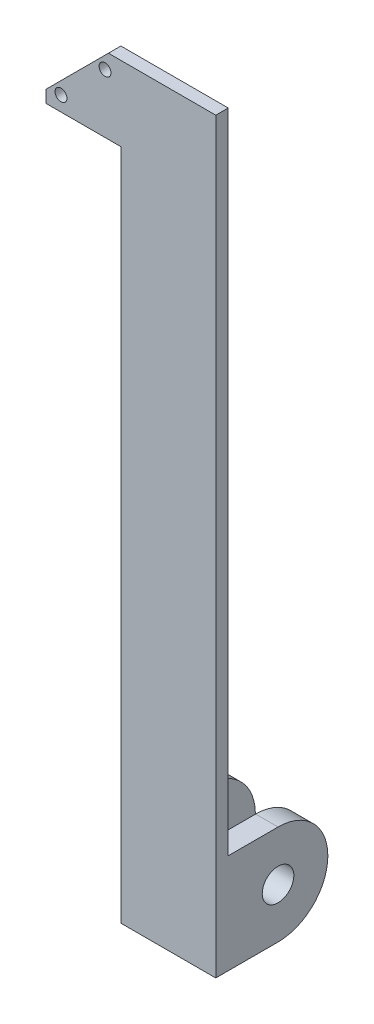
SolidWorks part; units mm, degrees
ref_plane "Front Plane" through (0, 0, 0) normal (0, 0, 1) x (1, 0, 0)
ref_plane "Top Plane" through (0, 0, 0) normal (0, 1, 0) x (1, 0, 0)
ref_plane "Right Plane" through (0, 0, 0) normal (1, 0, 0) x (0, 0, -1)
sketch "Sketch1" plane through (0, 0, 0) normal (0, 0, 1) x (1, 0, 0)
  line L0 (-30, 270) -> (0, 300)
  line L1 (0, 0) -> (38.1, 0)
  line L2 (0, 0) -> (0, 300)
  line L3 (0, 300) -> (38.1, 300)
  line L4 (38.1, 0) -> (38.1, 300)
  line L5 (0, 300) -> (-30, 300)
  line L6 (0, 300) -> (0, 270)
  line L7 (0, 270) -> (-30, 270)
  line L8 (-30, 300) -> (-30, 270)
  line L9 (-30, 275) -> (-5, 300)
  circle A0 centre (-6.364, 293.636) radius 2.3813
  circle A1 centre (-24.0416, 275.9584) radius 2.3813
  dimension "D5" = 4.7625
  dimension "D6" = 4.7625
  dimension "D1" = 300
  dimension "D2" = 38.1
  dimension "D3" = 30
  dimension "D4" = 30
  dimension "D7" = 25
  dimension "D8" = 9
  dimension "D9" = 5
  dimension "D10" = 5
extrude "Boss-Extrude1" add sketch "Sketch1" along normal blind 5 contours A1 L0 A0 L5 L9 L8 | A1 L0 L7 L2 A0 | L1 L4 L3 L2
sketch "Sketch4" plane through (0, 0, 0) normal (0, 0, -1) x (-1, 0, 0)
  line L0 (0, 0) -> (0, 270) construction
  line L1 (-38.1, 0) -> (0, 0)
  line L2 (-38.1, 0) -> (-38.1, 40)
  line L3 (-38.1, 40) -> (0, 40)
  line L4 (0, 0) -> (0, 40)
  line L6 (-29.1, 40) -> (-9, 40)
  line L7 (-29.1, 40) -> (-29.1, 0)
  line L8 (-29.1, 0) -> (-9, 0)
  line L9 (-9, 40) -> (-9, 0)
  dimension "D1" = 40
  dimension "D2" = 9
  dimension "D3" = 9
extrude "Boss-Extrude3" add sketch "Sketch4" along normal blind 40 contours L7 L3 M12 M13 | L3 L9 M13 M14
sketch "Sketch5" plane through (38.1, 0, 0) normal (1, 0, 0) x (0, 0, -1)
  line L0 (40, 40) -> (0, 0)
  line L1 (20.01, 0) -> (0, 0)
  line L2 (40, 19.99) -> (40, 20.01)
  line L3 (20.01, 40) -> (0, 40)
  line L4 (0, 0) -> (0, 40)
  circle A0 centre (20, 20) radius 6.35
  arc A1 (20.01, 0) -> (40, 19.99) centre (20.01, 19.99) ccw
  arc A2 (40, 20.01) -> (20.01, 40) centre (20.01, 20.01) ccw
  point P10 (40, 0)
  dimension "D1" = 12.7
  dimension "D2" = 19.99
extrude "Cut-Extrude2" cut sketch "Sketch5" against normal blind 40 contours A2 L0 M9 | A2 L0 M10 | L0 A0 | L0 A0 | A1 M8 M9
